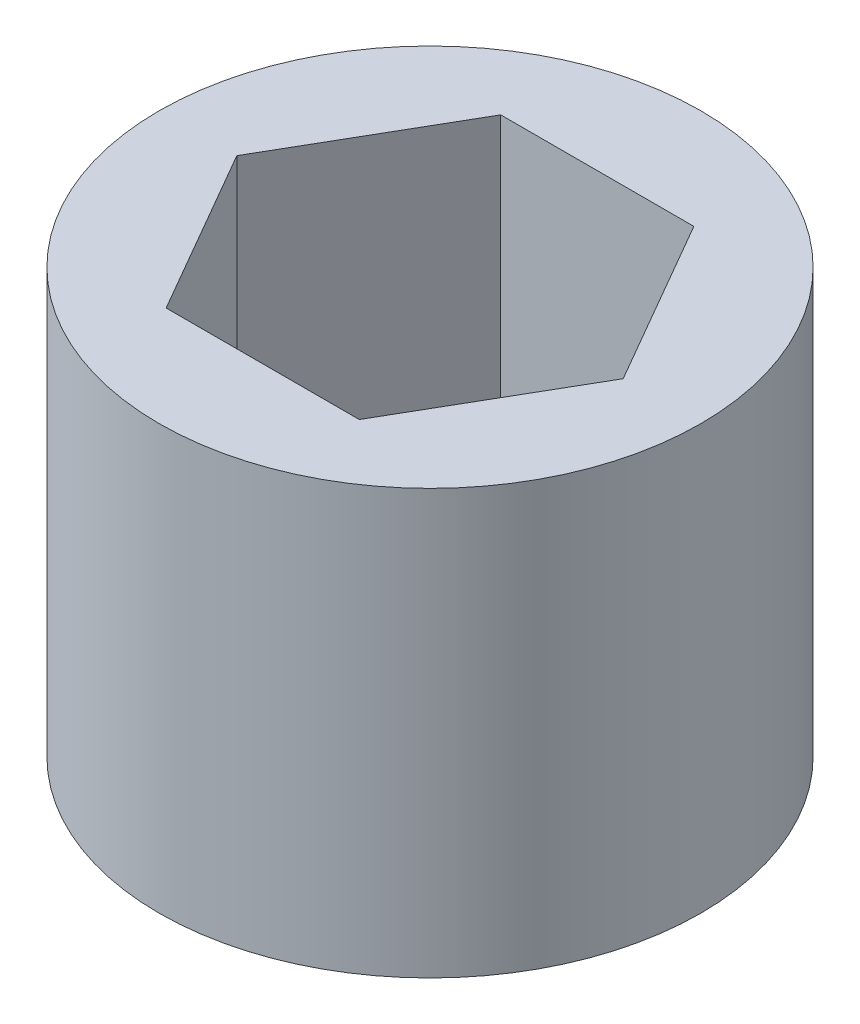
SolidWorks part; units mm, degrees
ref_plane "Front Plane" through (0, 0, 0) normal (0, 0, 1) x (1, 0, 0)
ref_plane "Top Plane" through (0, 0, 0) normal (0, 1, 0) x (1, 0, 0)
ref_plane "Right Plane" through (0, 0, 0) normal (1, 0, 0) x (0, 0, -1)
sketch "Sketch1" plane through (0, 0, 0) normal (0, 1, 0) x (1, 0, 0)
  line L1 (2.05, -3.5507) -> (4.1, 0)
  line L2 (4.1, 0) -> (2.05, 3.5507)
  line L3 (2.05, 3.5507) -> (-2.05, 3.5507)
  line L4 (-2.05, 3.5507) -> (-4.1, 0)
  line L5 (-4.1, 0) -> (-2.05, -3.5507)
  line L6 (-2.05, -3.5507) -> (2.05, -3.5507)
  circle A0 centre (0, 0) radius 3.5507 construction
  circle A1 centre (0, 0) radius 4.1
  circle A2 centre (0, 0) radius 5.75
  dimension "D1" = 8.2
  dimension "D2" = 11.5
extrude "Boss-Extrude1" add sketch "Sketch1" along normal blind 9 contours L5 A1 | L4 A1 | L3 A1 | L2 A1 | L1 A1 | L6 A1 | A2 A1
